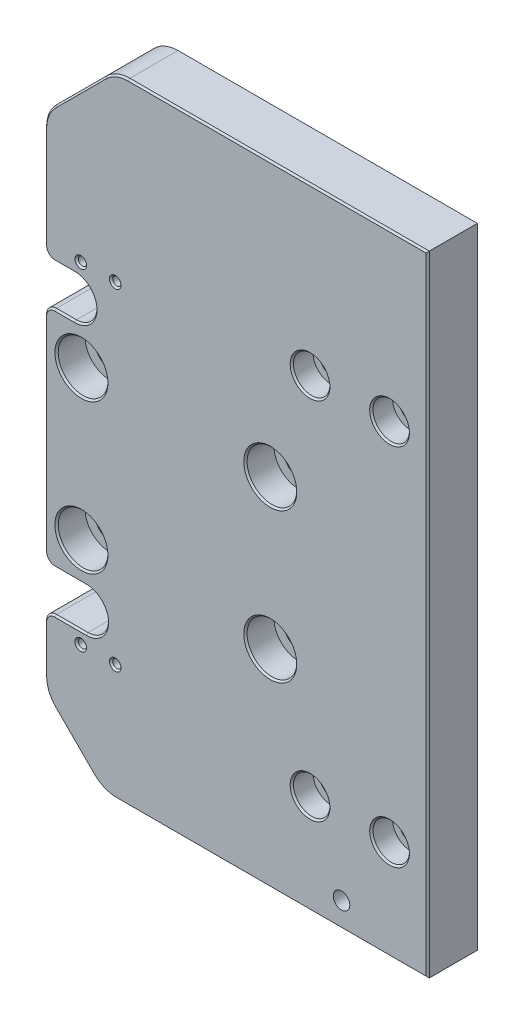
SolidWorks part; units mm, degrees
material "Alumina"
ref_plane "Plan de face" through (0, 0, 0) normal (0, 0, 1) x (1, 0, 0)
ref_plane "Plan de dessus" through (0, 0, 0) normal (0, 1, 0) x (1, 0, 0)
ref_plane "Plan de droite" through (0, 0, 0) normal (1, 0, 0) x (0, 0, -1)
sketch "Esquisse1" plane through (0, 0, 0) normal (0, 0, 1) x (1, 0, 0)
  line L0 (3, 169) -> (3, 17.5)
  line L1 (3, 169) -> (24, 190)
  line L3 (118.5, 190) -> (118.5, 0)
  line L4 (24, 190) -> (68.5, 190)
  line L5 (3, 17.5) -> (20.5, 0)
  line L6 (20.5, 0) -> (68.5, 0)
  line L9 (118.5, 0) -> (68.5, 0)
  line L13 (118.5, 190) -> (68.5, 190)
  dimension "D1" = 115.5
  dimension "D2" = 45
  dimension "D3" = 98
  dimension "D6" = 50
  dimension "D7" = 50
extrude "Boss.-Extru.1" add sketch "Esquisse1" along normal blind 15
hole_wizard "CBORE for M6 Hex Socket Head Cap Screw1" positions "Sketch1" profile "Sketch2" counterbore size "M6" standard "ISO" end condition through all
sketch "Sketch1" plane through (0, 0, 15) normal (0, 0, 1) x (1, 0, 0)
  line L1 (107, 140) -> (83, 140) construction
  line L2 (107, 140) -> (107, 30) construction
  line L3 (107, 30) -> (83, 30) construction
  line L4 (83, 140) -> (83, 30) construction
  line L5 (107, 140) -> (83, 30) construction
  line L6 (107, 30) -> (83, 140) construction
  line L7 (118.5, 190) -> (24, 190) construction
  point P1 (83, 30)
  point P4 (107, 140)
  point P5 (107, 30)
  point P6 (83, 140)
  dimension "D1" = 24
  dimension "D2" = 110
  dimension "40" = 50
sketch "Sketch2" plane through (83, 30, 15) normal (1, 0, 0) x (0, -1, 0)
  line L0 (0, 0) -> (0, 15)
  line L1 (0, 15) -> (3.3, 15)
  line L3 (3.3, 15) -> (3.3, 6.4)
  line L4 (3.3, 6.4) -> (5.5, 6.4)
  line L5 (5.5, 6.4) -> (5.5, 0)
  line L7 (5.5, 0) -> (0, 0)
  line L11 (0, -6.35) -> (0, 107.95) construction
  dimension "Thru Hole Dia." = 6.6
  dimension "Thru Hole Depth" = 15
  dimension "C'Bore Dia." = 11
  dimension "C'Bore Depth" = 6.4
hole_wizard "CBORE for M8 Hex Socket Head Cap Screw1" positions "Sketch7" profile "Sketch8" counterbore size "M8" standard "ISO" end condition through all
sketch "Sketch7" plane through (0, 0, 15) normal (0, 0, 1) x (1, 0, 0)
  line L1 (118.5, 0) -> (118.5, 190) construction
  line L2 (20.5, 0) -> (118.5, 0) construction
  point P3 (71, 107.5)
  point P6 (71, 62.5)
  point P9 (14, 62.5)
  point P12 (14, 107.5)
  dimension "D1" = 45
  dimension "D2" = 57
  dimension "D3" = 47.5
  dimension "D4" = 62.5
sketch "Sketch8" plane through (71, 107.5, 15) normal (1, 0, 0) x (0, -1, 0)
  line L0 (0, 0) -> (0, 15)
  line L1 (0, 15) -> (4.5, 15)
  line L3 (4.5, 15) -> (4.5, 8.6)
  line L4 (4.5, 8.6) -> (7.5, 8.6)
  line L5 (7.5, 8.6) -> (7.5, 0)
  line L7 (7.5, 0) -> (0, 0)
  line L11 (0, -6.35) -> (0, 107.95) construction
  dimension "Thru Hole Dia." = 9
  dimension "Thru Hole Depth" = 15
  dimension "C'Bore Dia." = 15
  dimension "C'Bore Depth" = 8.6
hole_wizard "Tap Drill for M6 Tap1" positions "Sketch12" profile "Sketch13" hole size "M6" standard "ISO" end condition through all
sketch "Sketch12" plane through (0, 0, 15) normal (0, 0, 1) x (1, 0, 0)
  point P0 (92.5, 7.5)
sketch "Sketch13" plane through (92.5, 7.5, 15) normal (1, 0, 0) x (0, -1, 0)
  line L0 (0, 0) -> (0, 15)
  line L1 (0, 15) -> (2.5, 15)
  line L2 (2.5, 15) -> (2.5, 0)
  line L5 (2.5, 0) -> (0, 0)
  line L11 (0, -6.35) -> (0, 107.95) construction
  dimension "Thru Hole Dia." = 5
  dimension "Thru Hole Depth" = 15
hole_wizard "Tap Drill for M3 Tap1" positions "Sketch14" profile "Sketch15" hole size "M3" standard "ISO" end condition through all
sketch "Sketch14" plane through (0, 0, 0) normal (0, 0, -1) x (-1, 0, 0)
  line L0 (-13.8, 35) -> (-24.2, 35) construction
  line L3 (-20.5, 0) -> (-118.5, 0) construction
  line L4 (-13.8, 135) -> (-24.2, 135) construction
  line L6 (-118.5, 190) -> (-24, 190) construction
  line L7 (-118.5, 0) -> (-118.5, 190) construction
  point P0 (-24.2, 35)
  point P2 (-13.8, 35)
  point P4 (-24.2, 135)
  point P6 (-13.8, 135)
  point P29 (-19, 35)
  dimension "D1" = 10.4
  dimension "D2" = 99.5
  dimension "D3" = 35
  dimension "D5" = 55
sketch "Sketch15" plane through (24.2, 35, 0) normal (1, 0, 0) x (0, 1, 0)
  line L0 (0, 0) -> (0, 15)
  line L1 (0, 15) -> (1.25, 15)
  line L2 (1.25, 15) -> (1.25, 0)
  line L5 (1.25, 0) -> (0, 0)
  line L11 (0, -6.35) -> (0, 107.95) construction
  dimension "Thru Hole Dia." = 2.5
  dimension "Thru Hole Depth" = 15
sketch "Sketch17" plane through (0, 0, 15) normal (0, 0, 1) x (1, 0, 0)
  line L5 (12, 125) -> (-6, 125) construction
  line L6 (3, 169) -> (3, 17.5) construction
  line L7 (12, 118.8) -> (-6, 118.8)
  line L8 (12, 131.2) -> (-6, 131.2)
  line L9 (15.5, 45) -> (-2.5, 45) construction
  line L10 (15.5, 38.8) -> (-2.5, 38.8)
  line L11 (15.5, 51.2) -> (-2.5, 51.2)
  arc A1 (12, 118.8) -> (12, 131.2) centre (12, 125) ccw
  arc A2 (-6, 131.2) -> (-6, 118.8) centre (-6, 125) ccw
  circle A3 centre (13.8, 135) radius 1.25 construction
  arc A4 (15.5, 38.8) -> (15.5, 51.2) centre (15.5, 45) ccw
  arc A5 (-2.5, 51.2) -> (-2.5, 38.8) centre (-2.5, 45) ccw
  circle A6 centre (13.8, 35) radius 1.25 construction
  point P8 (3, 125)
  point P17 (6.5, 45)
  dimension "D4" = 6.2
  dimension "D6" = 6.2
  dimension "D8" = 10
  dimension "D3" = 10
  dimension "D5" = 18
  dimension "D7" = 18
extrude "Cut-Extrude1" cut sketch "Sketch17" against normal through all
fillet "Fillet3" radius 10 4 edges at (24, 190, 7.5) (20.5, 0, 7.5) (3, 169, 7.5) (3, 17.5, 7.5)
fillet "Fillet4" radius 3 4 edges at (3, 118.8, 7.5) (3, 131.2, 7.5) (3, 51.2, 7.5) (3, 38.8, 7.5)
chamfer "Chamfer1" distance 0.5 angle 45 34 edges at (78.5, 107.5, 15) (88.5, 30, 15) (112.5, 30, 15) (112.5, 140, 15) (88.5, 140, 15) (78.5, 62.5, 15) (21.5, 62.5, 15) (21.5, 107.5, 15) (71.5711, 0, 15) (20.8153, 0.7612, 15) (11.75, 8.75, 15) (13.5, 179.5, 15) (24.3153, 189.2388, 15) (118.5, 95, 15) (73.3211, 190, 15) (12.55, 35, 15) (22.95, 35, 15) (12.55, 135, 15) (22.95, 135, 15) (3.7612, 17.8153, 15) (3, 28.7211, 15) (3, 149.5289, 15) (3.7612, 168.6847, 15) (3.8787, 37.9213, 15) (10.75, 38.8, 15) (21.7, 45, 15) (10.75, 51.2, 15) (3.8787, 52.0787, 15) (3, 85, 15) (3.8787, 117.9213, 15) (9, 118.8, 15) (18.2, 125, 15) (9, 131.2, 15) (3.8787, 132.0787, 15)
